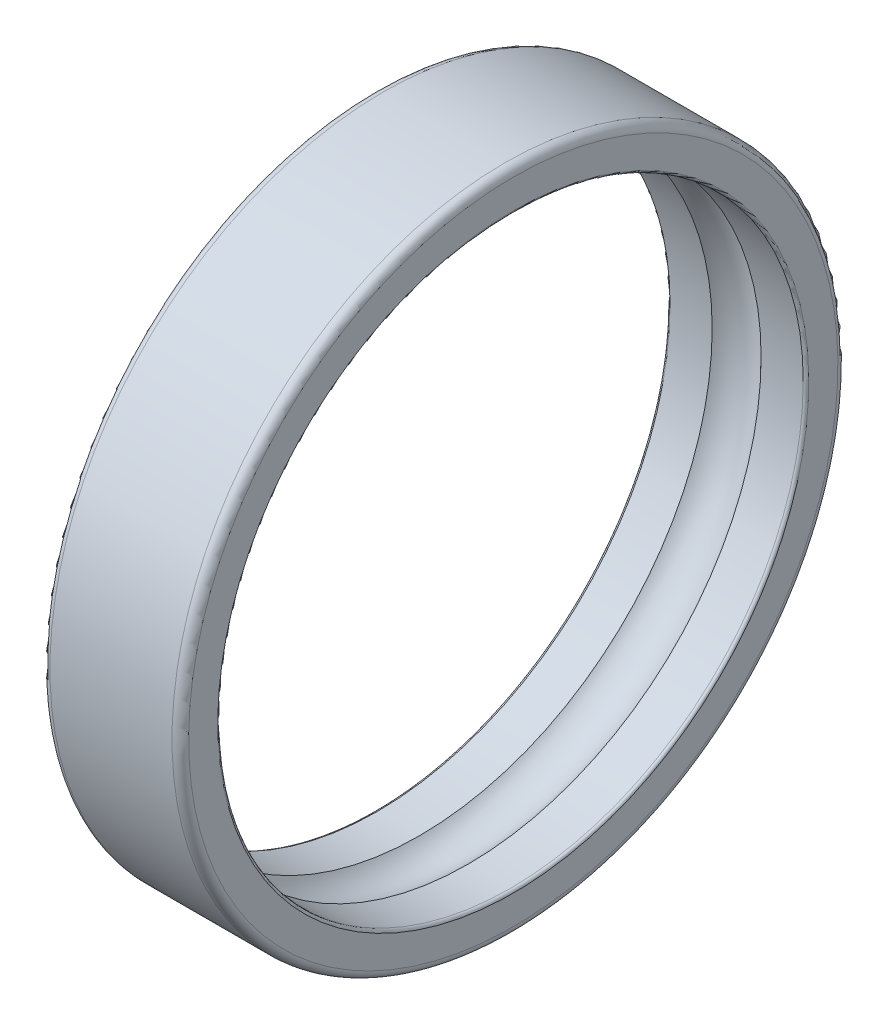
SolidWorks part; units mm, degrees
ref_plane "Front Plane" through (0, 0, 0) normal (0, 0, 1) x (1, 0, 0)
ref_plane "Top Plane" through (0, 0, 0) normal (0, 1, 0) x (1, 0, 0)
ref_plane "Right Plane" through (0, 0, 0) normal (1, 0, 0) x (0, 0, -1)
ref_plane "Plane1" through (0, 0, 0) normal (0, 0, 1) x (1, 0, 0)
sketch "Sketch1" plane through (0, 0, 0) normal (0, 0, 1) x (1, 0, 0)
  line L0 (0, 11.7) -> (0, 10.65)
  line L1 (0.1, 10.55) -> (1.6184, 10.55)
  line L2 (3.3816, 10.55) -> (4.9, 10.55)
  line L3 (5, 10.65) -> (5, 11.7)
  line L4 (4.7, 12) -> (0.3, 12)
  line L5 (5, 0) -> (0, 0) construction
  arc A0 (0, 10.65) -> (0.1, 10.55) centre (0.1, 10.65) ccw
  arc A1 (1.6184, 10.55) -> (3.3816, 10.55) centre (2.5, 9.75) cw
  arc A2 (4.9, 10.55) -> (5, 10.65) centre (4.9, 10.65) ccw
  arc A3 (5, 11.7) -> (4.7, 12) centre (4.7, 11.7) ccw
  arc A4 (0.3, 12) -> (0, 11.7) centre (0.3, 11.7) ccw
revolve "Revolve1" add sketch "Sketch1" angle 360 about L5
